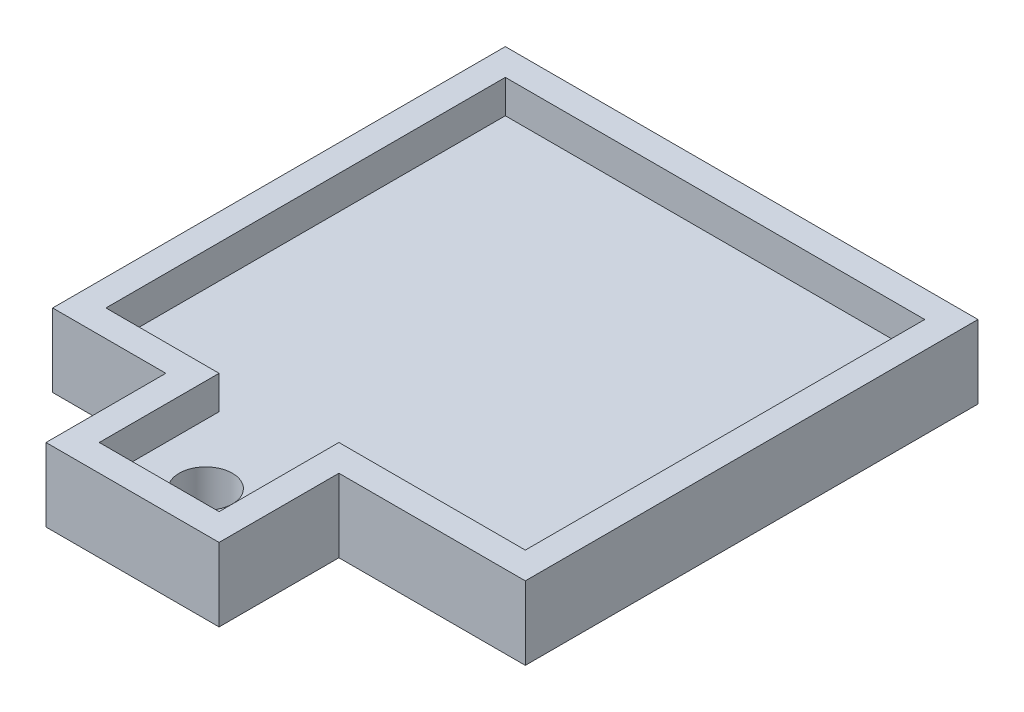
SolidWorks part; units mm, degrees
ref_plane "Front Plane" through (0, 0, 0) normal (0, 0, 1) x (1, 0, 0)
ref_plane "Top Plane" through (0, 0, 0) normal (0, 1, 0) x (1, 0, 0)
ref_plane "Right Plane" through (0, 0, 0) normal (1, 0, 0) x (0, 0, -1)
sketch "Sketch1" plane through (0, 0, 0) normal (0, 1, 0) x (1, 0, 0)
  line L1 (-157.5, 300) -> (157.5, 300)
  line L2 (-157.5, 300) -> (-157.5, 0)
  line L3 (157.5, 300) -> (157.5, 0)
  line L4 (-157.5, 0) -> (-72.5, 0)
  line L5 (-157.5, 0) -> (-72.5, 0)
  line L6 (-72.5, 0) -> (-72.5, -90)
  line L7 (-72.5, -90) -> (17.5, -90)
  line L8 (17.5, -90) -> (17.5, 0)
  line L9 (17.5, 0) -> (157.5, 0)
  circle A0 centre (-27.5, -55) radius 20
extrude "Boss-Extrude1" add sketch "Sketch1" along normal blind 30 contours L8 L9 L3 L1 L2 L4 L6 L7 A0
scale "Scale1" scale about centroid uniform scaling yes scale factor 0.1
sketch "Sketch2" plane through (0, 13.5, 0) normal (0, -1, 0) x (1, 0, 0)
  line L0 (-19.4213, -155.2607) -> (-19.4213, -121.2607)
  line L2 (14.0787, -153.2607) -> (14.0787, -123.2607)
  line L3 (16.0787, -155.2607) -> (-19.4213, -155.2607)
  line L5 (2.0787, -112.2607) -> (-10.9213, -112.2607)
  line L7 (16.0787, -155.2607) -> (16.0787, -121.2607)
  line L9 (16.0787, -121.2607) -> (2.0787, -121.2607)
  line L10 (-10.9213, -121.2607) -> (-19.4213, -121.2607)
  line L11 (2.0787, -121.2607) -> (2.0787, -112.2607)
  line L13 (-10.9213, -112.2607) -> (-10.9213, -121.2607)
  line L16 (14.0787, -123.2607) -> (0.0787, -123.2607)
  line L18 (0.0787, -123.2607) -> (0.0787, -114.2607)
  line L19 (0.0787, -114.2607) -> (-8.9213, -114.2607)
  line L20 (-8.9213, -114.2607) -> (-8.9213, -123.2607)
  line L21 (-8.9213, -123.2607) -> (-17.4213, -123.2607)
  line L22 (-17.4213, -123.2607) -> (-17.4213, -153.2607)
  line L23 (-17.4213, -153.2607) -> (14.0787, -153.2607)
extrude "Boss-Extrude2" add sketch "Sketch2" against normal blind 5.5
